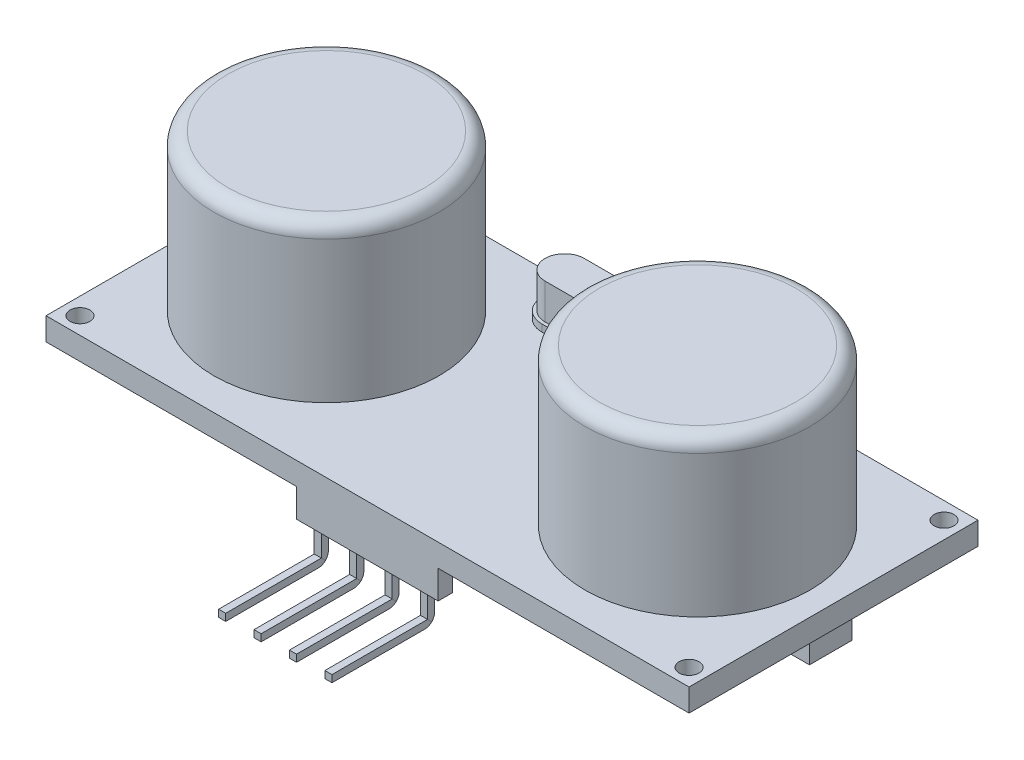
SolidWorks part; units mm, degrees
ref_plane "Alzado" through (0, 0, 0) normal (0, 0, 1) x (1, 0, 0)
ref_plane "Planta" through (0, 0, 0) normal (0, 1, 0) x (1, 0, 0)
ref_plane "Vista lateral" through (0, 0, 0) normal (1, 0, 0) x (0, 0, -1)
sketch "Croquis1" plane through (0, 0, 0) normal (0, 1, 0) x (1, 0, 0)
  line L1 (-22.7, 10.2) -> (22.7, 10.2)
  line L2 (-22.7, 10.2) -> (-22.7, -10.2)
  line L3 (-22.7, -10.2) -> (22.7, -10.2)
  line L4 (22.7, 10.2) -> (22.7, -10.2)
  line L5 (-22.7, 10.2) -> (22.7, -10.2) construction
  line L6 (-22.7, -10.2) -> (22.7, 10.2) construction
  point P0 (0, 0)
  dimension "D1" = 45.4
  dimension "D2" = 20.4
extrude "Saliente-Extruir1" add sketch "Croquis1" along normal blind 1.6
sketch "Croquis2" plane through (0, 1.6, 0) normal (0, 1, 0) x (1, 0, 0)
  line L5 (-21.5, 9) -> (21.5, -9) construction
  line L6 (-21.5, -9) -> (21.5, 9) construction
  circle A0 centre (-21.5, 9) radius 0.7
  circle A1 centre (21.5, 9) radius 0.7
  circle A2 centre (21.5, -9) radius 0.7
  circle A3 centre (-21.5, -9) radius 0.7
  point P0 (0, 0)
  dimension "D3" = 1.4
  dimension "D1" = 43
  dimension "D2" = 18
extrude "Cortar-Extruir1" cut sketch "Croquis2" against normal blind 1
sketch "Croquis3" plane through (0, 1.6, 0) normal (0, 1, 0) x (1, 0, 0)
  line L0 (0, 10.2) -> (0, -10.2) construction
  line L1 (22.7, 10.2) -> (-22.7, 10.2) construction
  line L2 (-22.7, -10.2) -> (22.7, -10.2) construction
  line L3 (-4.2022, 7.9196) -> (4.2022, 7.9196) construction
  line L4 (-4.2022, 9.5358) -> (4.2022, 9.5358)
  line L5 (-4.2022, 6.3033) -> (4.2022, 6.3033)
  line L6 (-4.2022, 7.9196) -> (4.2022, 7.9196) construction
  line L7 (-4.2022, 9.3049) -> (4.2022, 9.3049)
  line L8 (-4.2022, 6.5342) -> (4.2022, 6.5342)
  arc A0 (-4.2022, 9.5358) -> (-4.2022, 6.3033) centre (-4.2022, 7.9196) ccw
  arc A1 (4.2022, 6.3033) -> (4.2022, 9.5358) centre (4.2022, 7.9196) ccw
  arc A2 (-4.2022, 9.3049) -> (-4.2022, 6.5342) centre (-4.2022, 7.9196) ccw
  arc A3 (4.2022, 6.5342) -> (4.2022, 9.3049) centre (4.2022, 7.9196) ccw
  point P8 (0, 7.9196)
  point P15 (0, 7.9196)
extrude "Saliente-Extruir2" add sketch "Croquis3" along normal blind 0.5 contours L8 A3 L7 A2 | L5 A1 L4 A0
sketch "Croquis8" plane through (0, 1.6, 0) normal (0, 1, 0) x (1, 0, 0)
  line L0 (-4.2022, 9.3049) -> (4.2022, 9.3049) construction
  line L1 (-4.2022, 6.5342) -> (4.2022, 6.5342) construction
  line L2 (-4.2022, 9.3049) -> (4.2022, 9.3049)
  line L3 (-4.2022, 6.5342) -> (4.2022, 6.5342)
  arc A0 (4.2022, 6.5342) -> (4.2022, 9.3049) centre (4.2022, 7.9196) ccw construction
  arc A1 (-4.2022, 9.3049) -> (-4.2022, 6.5342) centre (-4.2022, 7.9196) ccw construction
  arc A2 (4.2022, 6.5342) -> (4.2022, 9.3049) centre (4.2022, 7.9196) ccw
  arc A3 (-4.2022, 9.3049) -> (-4.2022, 6.5342) centre (-4.2022, 7.9196) ccw
extrude "Saliente-Extruir3" add sketch "Croquis8" along normal blind 3
sketch "Croquis9" plane through (0, 1.6, 0) normal (0, 1, 0) x (1, 0, 0)
  line L0 (-21.05, 0) -> (21.05, 0) construction
  line L3 (-22.7, 10.2) -> (0, -10.2) construction
  line L4 (-22.7, -10.2) -> (22.7, -10.2) construction
  line L5 (0, -10.2) -> (22.7, 10.2) construction
  line L6 (-22.7, -10.2) -> (0, 10.2) construction
  line L7 (22.7, 10.2) -> (-22.7, 10.2) construction
  line L8 (0, 10.2) -> (22.7, -10.2) construction
  circle A0 centre (-13.1, 0) radius 7.95
  circle A1 centre (13.1, 0) radius 7.95
  point P2 (0, 0)
  dimension "D1" = 15.9
  dimension "D2" = 15.9
  dimension "D3" = 42.1
extrude "Saliente-Extruir4" add sketch "Croquis9" along normal blind 11
sketch "Croquis10" plane through (0, 0, 0) normal (0, -1, 0) x (1, 0, 0)
  line L0 (0, 10.2) -> (0, -10.2) construction
  line L1 (-22.7, 10.2) -> (22.7, 10.2) construction
  line L2 (22.7, -10.2) -> (-22.7, -10.2) construction
  line L3 (22.7, 0) -> (-22.7, 0) construction
  line L4 (22.7, 10.2) -> (22.7, -10.2) construction
  line L5 (-22.7, -10.2) -> (-22.7, 10.2) construction
  line L6 (-5.0127, 10.2) -> (4.9873, 10.2)
  line L7 (-5.0127, 10.2) -> (-5.0127, 9.2)
  line L8 (-5.0127, 9.2) -> (4.9873, 9.2)
  line L9 (4.9873, 9.2) -> (4.9873, 10.2)
  point P15 (-0.0127, 10.2)
  dimension "D1" = 10
  dimension "D2" = 1
extrude "Saliente-Extruir5" add sketch "Croquis10" along normal blind 2
sketch "Croquis11" plane through (0, -2, 0) normal (0, -1, 0) x (1, 0, 0)
  line L0 (-5.0127, 10.2) -> (-0.0127, 10.2) construction
  line L1 (4.9873, 10.2) -> (-5.0127, 10.2) construction
  line L2 (-2.5127, 10.2) -> (-2.5127, 9.2) construction
  line L3 (-5.0127, 9.2) -> (4.9873, 9.2) construction
  line L4 (-5.0127, 10.2) -> (-2.5127, 9.2) construction
  line L5 (-2.5127, 10.2) -> (-5.0127, 9.2) construction
sketch3d "Croquis3D1"
  line L0 (-3.7627, -2, 9.7) -> (-3.7627, -4, 9.7)
  line L1 (-5.0127, -2, 10.2) -> (-2.5127, -2, 9.2) construction
  line L2 (-3.7627, -4, 9.7) -> (-3.7627, -4, 16.7)
  dimension "D1" = 7
  dimension "D2" = 2
sketch "Croquis12" plane through (0, -2, 0) normal (0, -1, 0) x (1, 0, 0)
  line L1 (-4.0127, 9.95) -> (-3.5127, 9.95)
  line L2 (-4.0127, 9.95) -> (-4.0127, 9.45)
  line L3 (-4.0127, 9.45) -> (-3.5127, 9.45)
  line L4 (-3.5127, 9.95) -> (-3.5127, 9.45)
  line L5 (-4.0127, 9.95) -> (-3.5127, 9.45) construction
  line L6 (-4.0127, 9.45) -> (-3.5127, 9.95) construction
  point P0 (-3.7627, 9.7)
  dimension "D1" = 0.5
sweep "Barrer1" add profiles "Croquis12" path "Croquis3D1"
fillet "Redondeo4" radius 0.7 1 edges at (-3.7627, -4.25, 9.45)
pattern_linear "MatrizL1" count 4 spacing 2.5 along (1, 0, 0) of "Barrer1"
fillet "Redondeo5" radius 1 2 edges at (13.1, 12.6, 7.95) (-13.1, 12.6, 7.95)
sketch "Croquis13" plane through (0, 0, 0) normal (0, -1, 0) x (1, 0, 0)
  line L1 (-4.5, 1.5) -> (4.5, 1.5)
  line L2 (-4.5, 1.5) -> (-4.5, -1.5)
  line L3 (-4.5, -1.5) -> (4.5, -1.5)
  line L4 (4.5, 1.5) -> (4.5, -1.5)
  line L5 (-4.5, 1.5) -> (4.5, -1.5) construction
  line L6 (-4.5, -1.5) -> (4.5, 1.5) construction
  point P0 (0, 0)
  dimension "D1" = 9
  dimension "D2" = 3
extrude "Saliente-Extruir6" add sketch "Croquis13" along normal blind 1.5
pattern_linear "MatrizL2" count 2 spacing 18 along (1, 0, 0) of "Saliente-Extruir6"
sketch "Croquis14" plane through (0, 0, 0) normal (0, -1, 0) x (1, 0, 0)
  line L0 (-22.7, -10.2) -> (-22.7, 10.2) construction
  line L1 (-20.7, 4.2078) -> (-17.7, 4.2078)
  line L2 (-20.7, 4.2078) -> (-20.7, -4.7922)
  line L3 (-20.7, -4.7922) -> (-17.7, -4.7922)
  line L4 (-17.7, 4.2078) -> (-17.7, -4.7922)
  line L5 (-20.7, 4.2078) -> (-17.7, -4.7922) construction
  line L6 (-20.7, -4.7922) -> (-17.7, 4.2078) construction
  point P0 (-19.2, -0.2922)
  dimension "D1" = 3
  dimension "D2" = 2
  dimension "D3" = 9
extrude "Saliente-Extruir7" add sketch "Croquis14" along normal blind 1.5
fillet "Redondeo6" radius 0.7 3 edges at (3.7373, -4.25, 9.45) (1.2373, -4.25, 9.45) (-1.2627, -4.25, 9.45)
